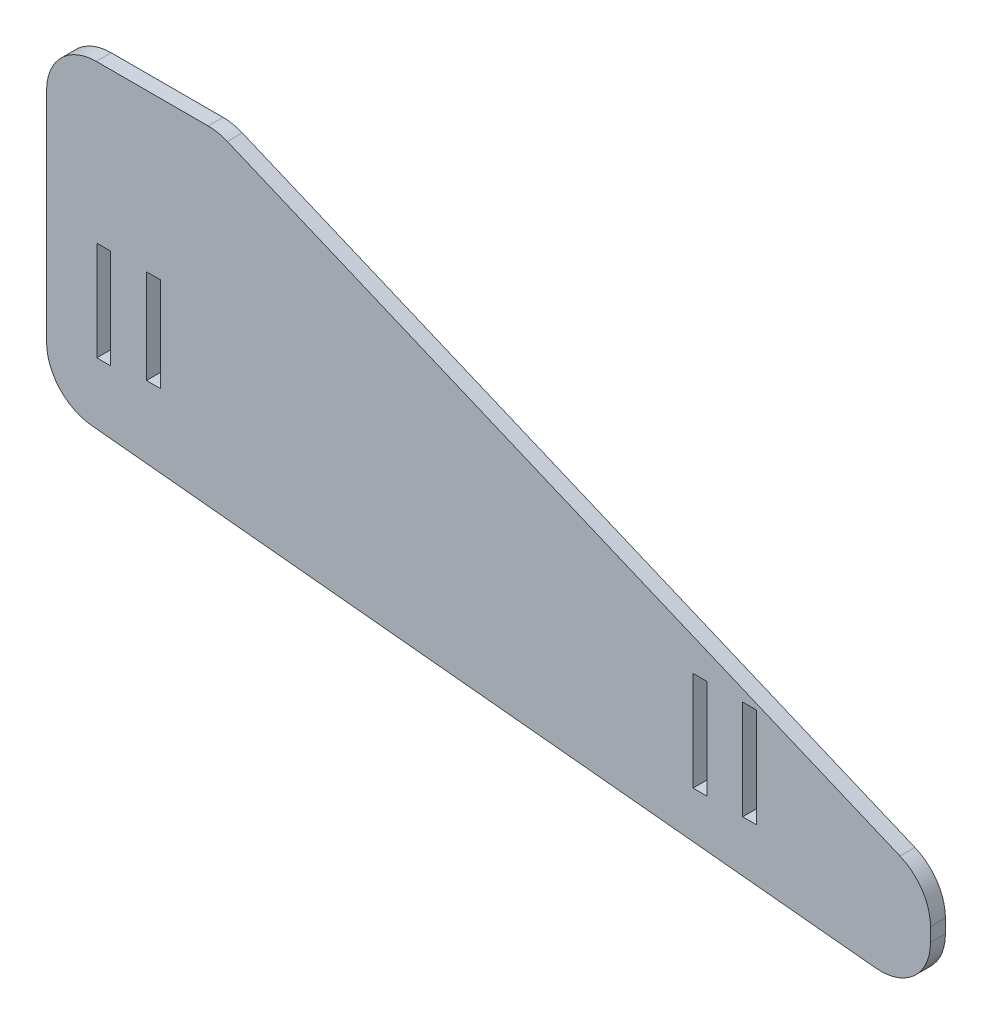
SolidWorks part; units mm, degrees
material "Acrylic (Medium-high impact)"
ref_plane "Front Plane" through (0, 0, 0) normal (0, 0, 1) x (1, 0, 0)
ref_plane "Top Plane" through (0, 0, 0) normal (0, 1, 0) x (1, 0, 0)
ref_plane "Right Plane" through (0, 0, 0) normal (1, 0, 0) x (0, 0, -1)
sketch "Sketch2" plane through (0, 0, 0) normal (0, 0, 1) x (1, 0, 0)
  line L0 (-20, 103.8171) -> (5, 103.8171)
  line L1 (5, 103.8171) -> (157.9, 39.6066)
  line L2 (157.9, 19.1266) -> (157.9, 39.6066)
  line L3 (157.9, 19.1266) -> (-20, 36.7792)
  line L4 (110, 53.1945) -> (113, 53.1945) construction
  line L5 (-17.1, 34.4817) -> (157.9, 17.1168) construction
  line L6 (-10, 103.8171) -> (-7, 103.8171) construction
  line L7 (-20, 103.8171) -> (-20, 36.7792)
  line L8 (-10, 48.1945) -> (-10, 68.1945) construction
  line L9 (157.9, 17.1168) -> (157.9, 15.6284) construction
  line L10 (110.1, 53.1945) -> (112.9, 53.1945)
  line L11 (110.1, 53.1945) -> (110.1, 33.1945)
  line L12 (110.1, 33.1945) -> (112.9, 33.1945)
  line L13 (112.9, 53.1945) -> (112.9, 33.1945)
  line L14 (113, 33.1945) -> (110, 33.1945) construction
  line L15 (123, 53.1945) -> (120, 53.1945) construction
  line L16 (120.1, 53.1945) -> (122.9, 53.1945)
  line L17 (120.1, 53.1945) -> (120.1, 33.1945)
  line L18 (-9.9, 68.1945) -> (-9.9, 48.1945)
  line L19 (-10, 68.1945) -> (-7, 68.1945) construction
  line L20 (-10, 48.1945) -> (-7, 48.1945) construction
  line L21 (-9.9, 48.1945) -> (-7.1, 48.1945)
  line L22 (-7.1, 48.1945) -> (-7.1, 68.1945)
  line L23 (-7.1, 68.1945) -> (-9.9, 68.1945)
  line L24 (0.1, 68.1945) -> (0.1, 49.2418)
  line L25 (0.1, 49.2418) -> (2.9, 49.2418)
  line L26 (2.9, 49.2418) -> (2.9, 68.1945)
  line L27 (2.9, 68.1945) -> (0.1, 68.1945)
  line L28 (3, 68.1945) -> (0, 68.1945) construction
  line L29 (120.1, 33.1945) -> (122.9, 33.1945)
  line L30 (122.9, 53.1945) -> (122.9, 33.1945)
  line L31 (123, 33.1945) -> (120, 33.1945) construction
  line L32 (110, 33.1945) -> (110, 53.1945) construction
  line L33 (113, 53.1945) -> (113, 33.1945) construction
  line L34 (123, 53.1945) -> (123, 33.1945) construction
  line L35 (120, 33.1945) -> (120, 53.1945) construction
  line L36 (3, 48.1945) -> (3, 68.1945) construction
  line L37 (0, 48.1945) -> (0, 68.1945) construction
  line L38 (-7, 48.1945) -> (-7, 68.1945) construction
  line L39 (3, 49.2418) -> (0, 49.2418) construction
  ellipse E0 centre (168.6969, 38.2343) end of major axis (182.5305, 44.0335) minor radius 6.9933 construction
  dimension "D1" = 25
  dimension "D2" = 10
  dimension "D3" = 2
  dimension "D4" = 0.1
  dimension "D5" = 0.1
  dimension "D6" = 0.1
  dimension "D7" = 0.1
  dimension "D8" = 0.1
  dimension "D9" = 0.1
  dimension "D10" = 0.1
  dimension "D11" = 0.1
extrude "Boss-Extrude1" add sketch "Sketch2" along normal blind 3
fillet "Fillet1" radius 10 3 edges at (157.9, 19.1266, 1.5) (157.9, 39.6066, 1.5) (-20, 36.7792, 1.5)
sketch "Sketch3" plane through (0, 0, 0) normal (0, 0, -1) x (-1, 0, 0)
  line L0 (-151.7719, 42.1801) -> (-5, 103.8171) construction
  line L1 (20, 103.8171) -> (-14.5249, 103.8171)
  line L2 (20, 103.8171) -> (20, 99.8171)
  line L3 (20, 99.8171) -> (-14.5249, 99.8171)
  line L4 (-14.5249, 103.8171) -> (-14.5249, 99.8171)
  dimension "D1" = 4
extrude "Cut-Extrude1" cut sketch "Sketch3" against normal blind 10
fillet "Fillet2" radius 10 2 edges at (14.5249, 99.8171, 1.5) (-20, 99.8171, 1.5)
